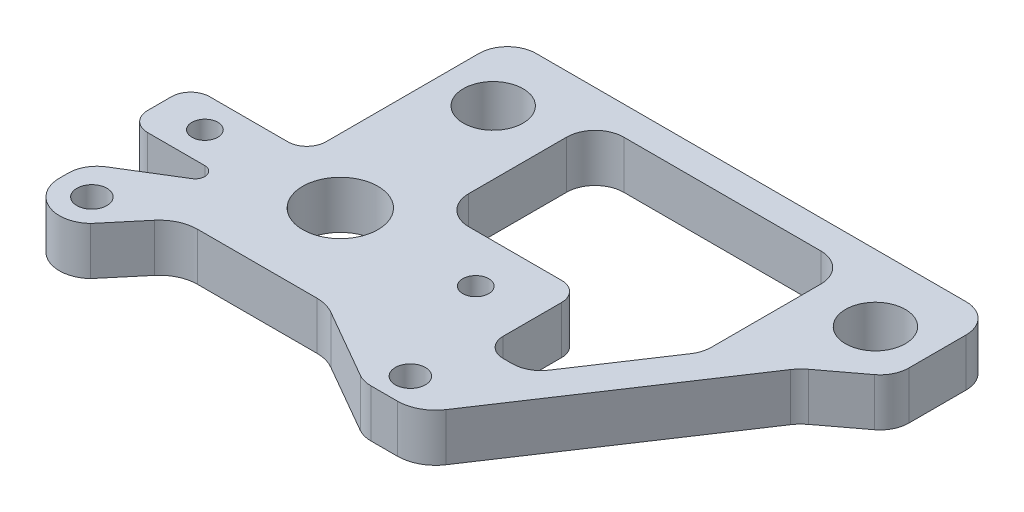
SolidWorks part; units mm, degrees
other "Markup1"
sketch "Sketch6" plane through (-23.3268, 0, -30.7975) normal (-0.0348, 0.9994, -0.0028) x (-0.9993, -0.0348, 0.0153)
sketch "Sketch7" plane through (-23.3268, 0, -30.7975) normal (-0.0348, 0.9994, -0.0028) x (-0.9993, -0.0348, 0.0153)
sketch "Sketch8" plane through (-23.3268, 0, -30.7975) normal (-0.0348, 0.9994, -0.0028) x (-0.9993, -0.0348, 0.0153)
sketch "Sketch10" plane through (-23.3268, 0, -30.7975) normal (-0.0348, 0.9994, -0.0028) x (-0.9993, -0.0348, 0.0153)
sketch "Sketch13" plane through (-23.3268, 0, -30.7975) normal (-0.0348, 0.9994, -0.0028) x (-0.9993, -0.0348, 0.0153)
sketch "Sketch15" plane through (-23.3268, 0, -30.7975) normal (-0.0348, 0.9994, -0.0028) x (-0.9993, -0.0348, 0.0153)
sketch "Sketch16" plane through (-23.3268, 0, -30.7975) normal (-0.0348, 0.9994, -0.0028) x (-0.9993, -0.0348, 0.0153)
sketch "Sketch17" plane through (-23.3268, 0, -30.7975) normal (-0.0348, 0.9994, -0.0028) x (-0.9993, -0.0348, 0.0153)
sketch "Sketch18" plane through (-23.3268, 0, -30.7975) normal (-0.0348, 0.9994, -0.0028) x (-0.9993, -0.0348, 0.0153)
sketch "Sketch19" plane through (-23.3268, 0, -30.7975) normal (-0.0348, 0.9994, -0.0028) x (-0.9993, -0.0348, 0.0153)
sketch "Sketch21" plane through (-23.3268, 0, -30.7975) normal (-0.0348, 0.9994, -0.0028) x (-0.9993, -0.0348, 0.0153)
sketch "Sketch23" plane through (-23.3268, 0, -30.7975) normal (-0.0348, 0.9994, -0.0028) x (-0.9993, -0.0348, 0.0153)
sketch "Sketch24" plane through (-23.3268, 0, -30.7975) normal (-0.0348, 0.9994, -0.0028) x (-0.9993, -0.0348, 0.0153)
sketch "Sketch25" plane through (-23.3268, 0, -30.7975) normal (-0.0348, 0.9994, -0.0028) x (-0.9993, -0.0348, 0.0153)
sketch "Sketch26" plane through (-23.3268, 0, -30.7975) normal (-0.0348, 0.9994, -0.0028) x (-0.9993, -0.0348, 0.0153)
sketch "Sketch27" plane through (-23.3268, 0, -30.7975) normal (-0.0348, 0.9994, -0.0028) x (-0.9993, -0.0348, 0.0153)
sketch "Sketch28" [suppressed] plane through (-23.3268, 0, -30.7975) normal (-0.0348, 0.9994, -0.0028) x (-0.9993, -0.0348, 0.0153)
sketch "Sketch29" plane through (-23.3268, 0, -30.7975) normal (-0.0348, 0.9994, -0.0028) x (-0.9993, -0.0348, 0.0153)
sketch "Sketch30" plane through (-23.3268, 0, -30.7975) normal (-0.0348, 0.9994, -0.0028) x (-0.9993, -0.0348, 0.0153)
sketch "Sketch32" plane through (-23.3268, 0, -30.7975) normal (-0.0348, 0.9994, -0.0028) x (-0.9993, -0.0348, 0.0153)
sketch "Sketch34" plane through (-23.3268, 0, -30.7975) normal (-0.0348, 0.9994, -0.0028) x (-0.9993, -0.0348, 0.0153)
sketch "Sketch35" plane through (-23.3268, 0, -30.7975) normal (-0.0348, 0.9994, -0.0028) x (-0.9993, -0.0348, 0.0153)
sketch "Sketch36" plane through (-23.3268, 0, -30.7975) normal (-0.0348, 0.9994, -0.0028) x (-0.9993, -0.0348, 0.0153)
sketch "Sketch37" plane through (-23.3268, 0, -30.7975) normal (-0.0348, 0.9994, -0.0028) x (-0.9993, -0.0348, 0.0153)
sketch "Sketch38" plane through (-23.3268, 0, -30.7975) normal (-0.0348, 0.9994, -0.0028) x (-0.9993, -0.0348, 0.0153)
sketch "Sketch39" plane through (-23.3268, 0, -30.7975) normal (-0.0348, 0.9994, -0.0028) x (-0.9993, -0.0348, 0.0153)
sketch "Sketch40" plane through (-23.3268, 0, -30.7975) normal (-0.0348, 0.9994, -0.0028) x (-0.9993, -0.0348, 0.0153)
sketch "Sketch41" [suppressed] plane through (-23.3268, 0, -30.7975) normal (-0.0348, 0.9994, -0.0028) x (-0.9993, -0.0348, 0.0153)
sketch "Sketch42" [suppressed] plane through (-23.3268, 0, -30.7975) normal (-0.0348, 0.9994, -0.0028) x (-0.9993, -0.0348, 0.0153)
sketch "Sketch43" plane through (-23.3268, 0, -30.7975) normal (-0.0348, 0.9994, -0.0028) x (-0.9993, -0.0348, 0.0153)
sketch "Sketch44" plane through (-23.3268, 0, -30.7975) normal (-0.0348, 0.9994, -0.0028) x (-0.9993, -0.0348, 0.0153)
sketch "Sketch45" plane through (-23.3268, 0, -30.7975) normal (-0.0348, 0.9994, -0.0028) x (-0.9993, -0.0348, 0.0153)
sketch "Sketch46" plane through (-23.3268, 0, -30.7975) normal (-0.0348, 0.9994, -0.0028) x (-0.9993, -0.0348, 0.0153)
sketch "Sketch47" plane through (-23.3268, 0, -30.7975) normal (-0.0348, 0.9994, -0.0028) x (-0.9993, -0.0348, 0.0153)
sketch "Sketch48" plane through (-23.3268, 0, -30.7975) normal (-0.0348, 0.9994, -0.0028) x (-0.9993, -0.0348, 0.0153)
sketch "Sketch49" [suppressed] plane through (-23.3268, 0, -30.7975) normal (-0.0348, 0.9994, -0.0028) x (-0.9993, -0.0348, 0.0153)
sketch "Sketch50" [suppressed] plane through (-23.3268, 0, -30.7975) normal (-0.0348, 0.9994, -0.0028) x (-0.9993, -0.0348, 0.0153)
sketch "Sketch51" plane through (-23.3268, 0, -30.7975) normal (-0.0348, 0.9994, -0.0028) x (-0.9993, -0.0348, 0.0153)
sketch "Sketch52" plane through (-23.3268, 0, -30.7975) normal (-0.0348, 0.9994, -0.0028) x (-0.9993, -0.0348, 0.0153)
sketch "Sketch53" plane through (-23.3268, 0, -30.7975) normal (-0.0348, 0.9994, -0.0028) x (-0.9993, -0.0348, 0.0153)
sketch "Sketch54" plane through (-23.3268, 0, -30.7975) normal (-0.0348, 0.9994, -0.0028) x (-0.9993, -0.0348, 0.0153)
sketch "Sketch55" plane through (-23.3268, 0, -30.7975) normal (-0.0348, 0.9994, -0.0028) x (-0.9993, -0.0348, 0.0153)
sketch "Sketch56" [suppressed] plane through (-23.3268, 0, -30.7975) normal (-0.0348, 0.9994, -0.0028) x (-0.9993, -0.0348, 0.0153)
sketch "Sketch57" [suppressed] plane through (-23.3268, 0, -30.7975) normal (-0.0348, 0.9994, -0.0028) x (-0.9993, -0.0348, 0.0153)
sketch "Sketch58" [suppressed] plane through (-23.3268, 0, -30.7975) normal (-0.0348, 0.9994, -0.0028) x (-0.9993, -0.0348, 0.0153)
sketch "Sketch59" [suppressed] plane through (-23.3268, 0, -30.7975) normal (-0.0348, 0.9994, -0.0028) x (-0.9993, -0.0348, 0.0153)
sketch "Sketch60" [suppressed] plane through (-23.3268, 0, -30.7975) normal (-0.0348, 0.9994, -0.0028) x (-0.9993, -0.0348, 0.0153)
sketch "Sketch61" plane through (-23.3268, 0, -30.7975) normal (-0.0348, 0.9994, -0.0028) x (-0.9993, -0.0348, 0.0153)
sketch "Sketch62" plane through (-23.3268, 0, -30.7975) normal (-0.0348, 0.9994, -0.0028) x (-0.9993, -0.0348, 0.0153)
sketch "Sketch63" plane through (-23.3268, 0, -30.7975) normal (-0.0348, 0.9994, -0.0028) x (-0.9993, -0.0348, 0.0153)
material "6061-T6 (SS)"
ref_plane "X-Y Datum" through (0, 0, 0) normal (0, 0, 1) x (1, 0, 0)
ref_plane "X-Z Datum" through (0, 0, 0) normal (0, 1, 0) x (1, 0, 0)
ref_plane "Y-Z Datum" through (0, 0, 0) normal (1, 0, 0) x (0, 0, -1)
other "Graphic1"
other "Graphic (Closed) -1"
other "Graphic (Closed) -2"
sketch "Sketch2" plane through (0, 0, 0) normal (0, 1, 0) x (1, 0, 0)
  line L0 (48.6426, -18.7325) -> (-23.0162, -18.7325)
  line L1 (24.0125, -14.7036) -> (25.7865, -13.7801) construction
  line L2 (0, 0) -> (105.5557, -202.7707) construction
  line L3 (11.142, -21.4036) -> (-3.5026, -29.027) construction
  line L4 (0, 0) -> (0, -121.3797) construction
  line L5 (-3.5026, -29.027) -> (90.9112, -210.3941) construction
  line L6 (90.9112, -210.3941) -> (105.5557, -202.7707) construction
  line L7 (11.142, -21.4036) -> (24.0125, -14.7036) construction
  line L11 (-12.7, 30.7975) -> (57.15, 30.7975)
  line L12 (57.15, 13.0175) -> (57.15, 30.7975)
  line L13 (57.15, 13.0175) -> (-12.7, 13.0175) construction
  line L15 (44.7685, -18.0975) -> (44.7685, -11.3157) construction
  line L16 (44.7685, -18.0975) -> (34.8625, -18.0975) construction
  line L18 (44.7685, 9.8425) -> (34.8625, 9.8425) construction
  line L20 (44.7685, -11.3157) -> (49.8485, -11.3157) construction
  line L21 (49.8485, -11.3157) -> (49.8485, 3.0607) construction
  line L22 (49.8485, 3.0607) -> (44.7685, 3.0607) construction
  line L23 (44.7685, 3.0607) -> (44.7685, 9.8425) construction
  line L24 (34.8625, -18.0975) -> (34.8625, 9.8425) construction
  line L25 (48.6426, -18.7325) -> (57.15, 13.0175)
  line L26 (-12.7, 30.7975) -> (-12.7, 13.0175)
  line L28 (-12.5603, 0) -> (-16.51, -40.5272) construction
  line L30 (-23.0162, -18.7325) -> (-12.7, 13.0175)
  circle A0 centre (0, 0) radius 3.175
  circle A1 centre (24.0125, -14.7036) radius 2
  circle A2 centre (-1.5875, 21.9075) radius 3.9688
  circle A3 centre (49.2125, 21.9075) radius 3.9687
  circle A4 centre (39.8485, -4.1275) radius 5.1
  circle A5 centre (24.0125, -14.7036) radius 3.175 construction
  circle A6 centre (39.8485, -14.6275) radius 1.6
  circle A7 centre (39.8485, 6.3725) radius 1.6
  circle A8 centre (-17.2047, -14.9225) radius 3.175 construction
  circle A9 centre (-17.2047, -14.9225) radius 2
  point P9 (11.142, -21.4036)
  point P30 (49.8485, -4.1275)
  point P31 (34.8625, -4.1275)
  dimension "D1" = 6.35
  dimension "D8" = 4
  dimension "D10" = 7.9375
  dimension "D11" = 7.9375
  dimension "D16" = 27.94
  dimension "D23" = 10.2
  dimension "D20" = 6.35
  dimension "D30" = 3.2
  dimension "D32" = 3.2
  dimension "D34" = 6.35
  dimension "D35" = 4
  dimension "D3" = 13.0175
  dimension "D4" = 16.51
  dimension "D5" = 228.6
  dimension "D6" = 24.13
  dimension "D7" = 27.5
  dimension "D9" = 16.51
  dimension "D12" = 8.89
  dimension "D13" = 69.85
  dimension "D14" = 7.9375
  dimension "D15" = 31.75
  dimension "D17" = 17.78
  dimension "D18" = 3.175
  dimension "D19" = 14.986
  dimension "D21" = 5.08
  dimension "D22" = 14.3764
  dimension "D24" = 10
  dimension "D25" = 36.83
  dimension "D26" = 50.8
  dimension "D27" = 165
  dimension "D28" = 12.7
  dimension "D29" = 17.3015
  dimension "D31" = 10.5
  dimension "D33" = 10.5
  dimension "D36" = 162
extrude "Boss-Extrude1" [suppressed] add sketch "Sketch2" against normal blind 6.35
ref_point "Point1" [suppressed]
sketch "Sketch3" [suppressed] plane through (0, 0, 0) normal (0, 1, 0) x (1, 0, 0)
  line L0 (39.9681, 6.3725) -> (39.9681, -4.1275) construction
  line L1 (57.2697, 12.9663) -> (-12.5803, 12.9663) construction
  line L5 (39.9681, -4.1275) -> (39.9681, -14.6275) construction
  line L6 (42.0297, -18.7325) -> (20.4164, -18.7325)
  line L7 (57.2697, 12.9663) -> (57.2697, 30.7975)
  line L8 (57.2697, 30.7975) -> (-12.5803, 30.7975)
  line L9 (-12.5803, 30.7975) -> (-12.5803, 12.9663)
  line L10 (40.938, 24.6176) -> (16.9472, 10.7666)
  line L11 (13.3942, 11.8528) -> (6.9035, 25.1608)
  line L12 (8.045, 26.9875) -> (40.303, 26.9875)
  line L13 (57.2697, 12.9663) -> (48.3797, 12.9663)
  line L14 (48.3797, 12.9663) -> (48.3797, -12.3825)
  line L16 (-23.0162, -18.7325) -> (48.6426, -18.7325) construction
  line L18 (16.6064, -14.8627) -> (10.2787, -14.8627)
  line L21 (-8.965, -15.5427) -> (-15.106, -18.7325)
  line L24 (-21.1701, -13.6017) -> (-12.5803, 12.9663)
  line L29 (17.8764, -16.1925) -> (17.8764, -16.1327)
  circle A0 centre (0.1197, 0) radius 3.175
  circle A1 centre (-1.4678, 21.9075) radius 3.9688
  circle A2 centre (49.3322, 21.9075) radius 3.9687
  circle A3 centre (39.9681, -4.1275) radius 5.1
  circle A4 centre (39.9681, -14.6275) radius 1.6
  circle A5 centre (39.9681, 6.3725) radius 1.6
  circle A6 centre (24.1322, -14.7036) radius 2
  circle A7 centre (-17.085, -14.9225) radius 2
  arc A8 (13.3942, 11.8528) -> (16.9472, 10.7666) centre (15.6772, 12.9663) ccw
  arc A9 (8.045, 26.9875) -> (6.9035, 25.1608) centre (8.045, 25.7175) ccw
  arc A10 (40.938, 24.6176) -> (40.303, 26.9875) centre (40.303, 25.7175) ccw
  arc A11 (10.2787, -14.8627) -> (-8.965, -15.5427) centre (0.1197, 0) cw
  arc A12 (-15.106, -18.7325) -> (-21.1701, -13.6017) centre (-17.085, -14.9225) cw
  arc A13 (42.0297, -18.7325) -> (48.3797, -12.3825) centre (42.0297, -12.3825) ccw
  arc A14 (20.4164, -18.7325) -> (17.8764, -16.1925) centre (20.4164, -16.1925) cw
  arc A15 (16.6064, -14.8627) -> (17.8764, -16.1327) centre (16.6064, -16.1327) cw
  dimension "D1" = 6.35
  dimension "D4" = 7.9375
  dimension "D9" = 10.2
  dimension "D10" = 3.2
  dimension "D11" = 4
  dimension "D21" = 2.54
  dimension "D22" = 1.27
  dimension "D3" = 6.35
  dimension "D28" = 2.54
  dimension "D29" = 1.27
  dimension "D2" = 7.9375
  dimension "D5" = 50.8
  dimension "D6" = 21.9075
  dimension "D7" = 1.5875
  dimension "D8" = 8.89
  dimension "D12" = 10.5
  dimension "D13" = 17.2047
  dimension "D14" = 24.0125
  dimension "D15" = 14.7036
  dimension "D16" = 39.8485
  dimension "D17" = 4.1275
  dimension "D18" = 14.9225
  dimension "D19" = 69.85
  dimension "D20" = 3.81
  dimension "D23" = 30
  dimension "D24" = 64
  dimension "D25" = 32.258
  dimension "D26" = 15.5575
  dimension "D27" = 25.3488
  dimension "D30" = 8.89
sketch "Sketch4" plane through (0, 0, 0) normal (0, 1, 0) x (1, 0, 0)
  line L0 (39.8485, 6.3725) -> (39.8485, -4.1275) construction
  line L1 (56.1975, 13.0175) -> (-8.5725, 13.0175) construction
  line L2 (39.8485, -4.1275) -> (39.8485, -14.6275) construction
  line L3 (28.7355, -18.4375) -> (22.4839, -18.4375)
  line L5 (52.3875, 30.7975) -> (-4.7625, 30.7975)
  line L6 (-8.5725, 26.9875) -> (-8.5725, 12.6075)
  line L43 (48.9856, 12.0279) -> (54.6804, 16.3193)
  line L44 (56.1975, 19.3621) -> (56.1975, 26.9875)
  line L50 (-17.78, -15.24) -> (0, 0) construction
  line L58 (20.5837, -17.9298) -> (10.1629, -11.9335)
  line L59 (0, 0) -> (0, 5.6144) construction
  line L64 (48.9856, 12.0279) -> (28.7355, -18.4375)
  line L65 (6.8824, 26.9875) -> (40.693, 26.9875)
  line L66 (6.8824, 26.9875) -> (6.8824, 6.3725)
  line L70 (31.4047, -6.5013) -> (40.693, 7.4726)
  line L74 (40.693, 26.9875) -> (40.693, 7.4726)
  line L75 (6.8824, 6.3725) -> (25.5858, 6.3725)
  line L76 (10.1629, -11.9335) -> (-9.3997, -11.9335)
  line L77 (-9.3997, -11.9335) -> (-14.8229, -18.3866)
  line L78 (-24.0303, 4.1275) -> (-8.5725, 4.1275)
  line L79 (-8.5725, 4.1275) -> (-8.5725, 12.6075)
  line L82 (25.5858, 6.3725) -> (25.5858, -6.5013)
  line L83 (25.5858, -6.5013) -> (31.4047, -6.5013)
  line L84 (-24.0303, -4.1275) -> (-9.3997, -4.1275)
  line L85 (-9.3997, -4.1275) -> (-22.098, -11.9335)
  line L86 (-24.0303, 4.1275) -> (-24.0303, -4.1275)
  line L87 (-22.098, -11.9335) -> (-22.098, -15.24)
  circle A0 centre (0, 0) radius 5
  circle A1 centre (-1.5875, 21.9075) radius 3.9688
  circle A2 centre (49.2125, 21.9075) radius 3.9687
  circle A6 centre (24.0125, -14.7036) radius 2
  circle A7 centre (-17.78, -15.24) radius 2
  arc A12 (-14.8229, -18.3866) -> (-22.098, -15.24) centre (-17.78, -15.24) cw
  arc A19 (-8.5725, 26.9875) -> (-4.7625, 30.7975) centre (-4.7625, 26.9875) cw
  arc A20 (52.3875, 30.7975) -> (56.1975, 26.9875) centre (52.3875, 26.9875) cw
  circle A33 centre (24.0125, -14.7036) radius 3.5 construction
  arc A45 (56.1975, 19.3621) -> (54.6804, 16.3193) centre (52.3875, 19.3621) cw
  arc A53 (22.4839, -18.4375) -> (20.5837, -17.9298) centre (22.4839, -14.6275) cw
  circle A55 centre (0, 0) radius 18 construction
  circle A57 centre (18, 0) radius 1.7272
  circle A58 centre (-18, 0) radius 1.7272
  point P30 (21.466, -18.4375)
  point P36 (9.3466, -11.4637)
  point P58 (-8.5725, 30.7975)
  point P77 (56.1975, 17.4625)
  dimension "D1" = 10
  dimension "D2" = 7.9375
  dimension "D7" = 8.255
  dimension "D8" = 4
  dimension "D19" = 15.1072
  dimension "D20" = 6.9738
  dimension "D25" = 3.81
  dimension "D26" = 7
  dimension "D27" = 209.917
  dimension "D31" = 3.4544
  dimension "D33" = 4.318
  dimension "D37" = 15.4578
  dimension "D38" = 31.58
  dimension "D39" = 15.5045
  dimension "D23" = 3.81
  dimension "D32" = 3.81
  dimension "D46" = 14.9057
  dimension "D45" = 3.81
  dimension "D18" = 20.615
  dimension "D29" = 3.81
  dimension "D30" = 36
  dimension "D34" = 12.8738
  dimension "D35" = 4.3845
  dimension "D41" = 18.7034
  dimension "D42" = 7.3154
  dimension "D43" = 42.731
  dimension "D44" = 8.4293
  dimension "D3" = 50.8
  dimension "D4" = 21.9075
  dimension "D5" = 1.5875
  dimension "D9" = 10.5
  dimension "D10" = 24.0125
  dimension "D11" = 14.7036
  dimension "D12" = 39.8485
  dimension "D13" = 4.1275
  dimension "D14" = 15.24
  dimension "D15" = 17.78
  dimension "D16" = 6.985
  dimension "D17" = 8.89
  dimension "D21" = 17.78
  dimension "D22" = 229.956
  dimension "D24" = 236.388
  dimension "D28" = 30.4654
  dimension "D36" = 9.525
  dimension "D40" = 127
  dimension "D60" = 6.985
extrude "Boss-Extrude2" add sketch "Sketch4" against normal blind 6.35
ref_point "Point2"
ref_point "Point3"
ref_point "Point4"
other "Graphic2" [suppressed]
other "Graphic (Closed) -3"
other "Graphic (Closed) -4"
other "Graphic (Closed) -5"
fillet "Fillet1" radius 5.08 2 edges at (48.9856, -3.175, -12.0279) (28.7355, -3.175, 18.4375)
fillet "Fillet7" radius 3.81 4 edges at (6.8824, -3.175, -6.3725) (40.693, -3.175, -7.4726) (40.693, -3.175, -26.9875) (6.8824, -3.175, -26.9875)
fillet "Fillet9" radius 5.08 2 edges at (10.1629, -3.175, 11.9335) (-9.3997, -3.175, 11.9335)
fillet "Fillet10" radius 1.27 1 edges at (-9.3997, -3.175, 4.1275)
fillet "Fillet11" radius 3.81 1 edges at (-22.098, -3.175, 11.9335)
fillet "Fillet12" radius 2.54 5 edges at (25.5858, -3.175, 6.5013) (25.5858, -3.175, -6.3725) (-8.5725, -3.175, -4.1275) (-24.0303, -3.175, -4.1275) (-24.0303, -3.175, 4.1275)
fillet "Fillet13" radius 3.81 1 edges at (31.4047, -3.175, 6.5013)
